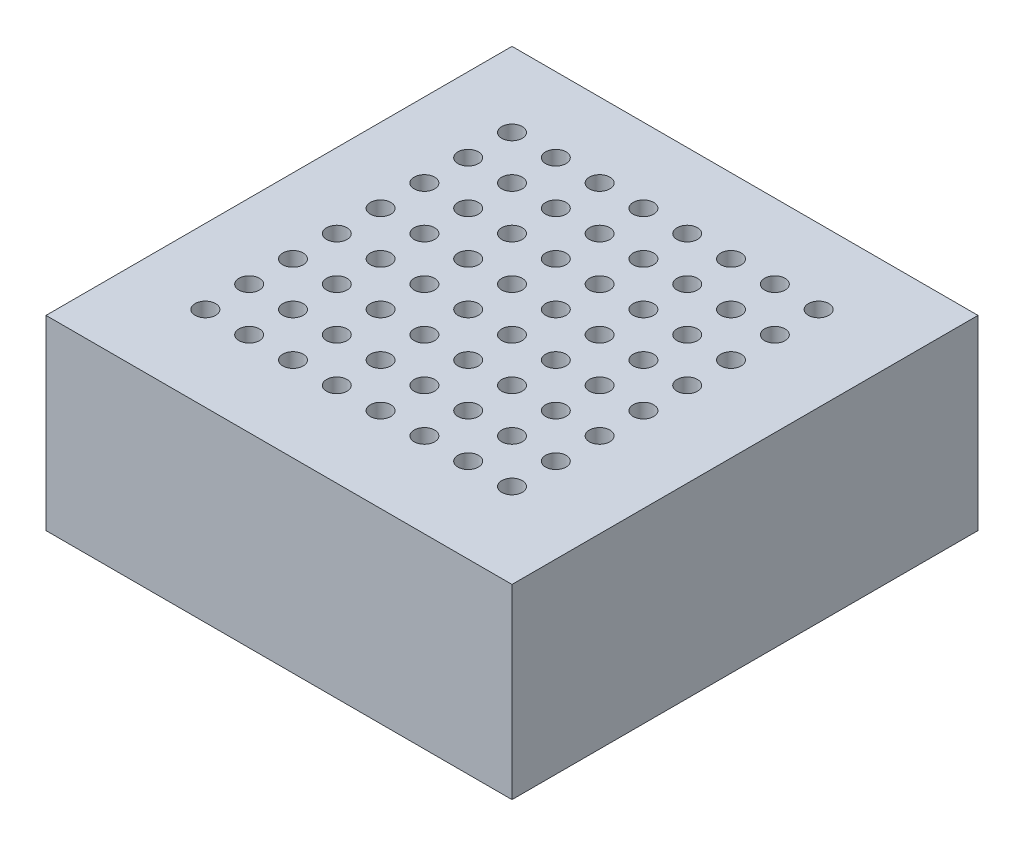
SolidWorks part; units mm, degrees
ref_plane "Front Plane" through (0, 0, 0) normal (0, 0, 1) x (1, 0, 0)
ref_plane "Top Plane" through (0, 0, 0) normal (0, 1, 0) x (1, 0, 0)
ref_plane "Right Plane" through (0, 0, 0) normal (1, 0, 0) x (0, 0, -1)
sketch "Sketch1" plane through (0, 0, 0) normal (0, 1, 0) x (1, 0, 0)
  line L1 (-12.5, 12.5) -> (12.5, 12.5)
  line L2 (-12.5, 12.5) -> (-12.5, -12.5)
  line L3 (-12.5, -12.5) -> (12.5, -12.5)
  line L4 (12.5, 12.5) -> (12.5, -12.5)
  line L5 (-11, 11) -> (11, 11) construction
  line L6 (-11, 11) -> (-11, -11) construction
  line L7 (-11, -11) -> (11, -11) construction
  line L8 (11, 11) -> (11, -11) construction
  circle A0 centre (-8.5, 8.5) radius 0.55
  circle A1 centre (-6.15, 8.5) radius 0.55
  circle A2 centre (-3.8, 8.5) radius 0.55
  circle A3 centre (-1.45, 8.5) radius 0.55
  circle A4 centre (0.9, 8.5) radius 0.55
  circle A5 centre (3.25, 8.5) radius 0.55
  circle A6 centre (5.6, 8.5) radius 0.55
  circle A7 centre (7.95, 8.5) radius 0.55
  circle A8 centre (-6.15, 6.15) radius 0.55
  circle A9 centre (-3.8, 6.15) radius 0.55
  circle A10 centre (-1.45, 6.15) radius 0.55
  circle A11 centre (0.9, 6.15) radius 0.55
  circle A12 centre (3.25, 6.15) radius 0.55
  circle A13 centre (5.6, 6.15) radius 0.55
  circle A14 centre (7.95, 6.15) radius 0.55
  circle A15 centre (-6.15, 3.8) radius 0.55
  circle A16 centre (-3.8, 3.8) radius 0.55
  circle A17 centre (-1.45, 3.8) radius 0.55
  circle A18 centre (0.9, 3.8) radius 0.55
  circle A19 centre (3.25, 3.8) radius 0.55
  circle A20 centre (5.6, 3.8) radius 0.55
  circle A21 centre (7.95, 3.8) radius 0.55
  circle A22 centre (-6.15, 1.45) radius 0.55
  circle A23 centre (-3.8, 1.45) radius 0.55
  circle A24 centre (-1.45, 1.45) radius 0.55
  circle A25 centre (0.9, 1.45) radius 0.55
  circle A26 centre (3.25, 1.45) radius 0.55
  circle A27 centre (5.6, 1.45) radius 0.55
  circle A28 centre (7.95, 1.45) radius 0.55
  circle A29 centre (-6.15, -0.9) radius 0.55
  circle A30 centre (-3.8, -0.9) radius 0.55
  circle A31 centre (-1.45, -0.9) radius 0.55
  circle A32 centre (0.9, -0.9) radius 0.55
  circle A33 centre (3.25, -0.9) radius 0.55
  circle A34 centre (5.6, -0.9) radius 0.55
  circle A35 centre (7.95, -0.9) radius 0.55
  circle A36 centre (-6.15, -3.25) radius 0.55
  circle A37 centre (-3.8, -3.25) radius 0.55
  circle A38 centre (-1.45, -3.25) radius 0.55
  circle A39 centre (0.9, -3.25) radius 0.55
  circle A40 centre (3.25, -3.25) radius 0.55
  circle A41 centre (5.6, -3.25) radius 0.55
  circle A42 centre (7.95, -3.25) radius 0.55
  circle A43 centre (-6.15, -5.6) radius 0.55
  circle A44 centre (-3.8, -5.6) radius 0.55
  circle A45 centre (-1.45, -5.6) radius 0.55
  circle A46 centre (0.9, -5.6) radius 0.55
  circle A47 centre (3.25, -5.6) radius 0.55
  circle A48 centre (5.6, -5.6) radius 0.55
  circle A49 centre (7.95, -5.6) radius 0.55
  circle A50 centre (-6.15, -7.95) radius 0.55
  circle A51 centre (-3.8, -7.95) radius 0.55
  circle A52 centre (-1.45, -7.95) radius 0.55
  circle A53 centre (0.9, -7.95) radius 0.55
  circle A54 centre (3.25, -7.95) radius 0.55
  circle A55 centre (5.6, -7.95) radius 0.55
  circle A56 centre (7.95, -7.95) radius 0.55
  circle A57 centre (-8.5, 6.15) radius 0.55
  circle A58 centre (-8.5, 3.8) radius 0.55
  circle A59 centre (-8.5, 1.45) radius 0.55
  circle A60 centre (-8.5, -0.9) radius 0.55
  circle A61 centre (-8.5, -3.25) radius 0.55
  circle A62 centre (-8.5, -5.6) radius 0.55
  circle A63 centre (-8.5, -7.95) radius 0.55
  point P11 (0, 0)
  dimension "D9" = 8
  dimension "D11" = 4
  dimension "D1" = 12.5
  dimension "D2" = 12.5
  dimension "D3" = 12.5
  dimension "D4" = 12.5
  dimension "D5" = 11
  dimension "D6" = 11
  dimension "D7" = 11
  dimension "D8" = 11
  dimension "D12" = 2.5
  dimension "D10" = 8
extrude "Boss-Extrude1" add sketch "Sketch1" along normal blind 10
